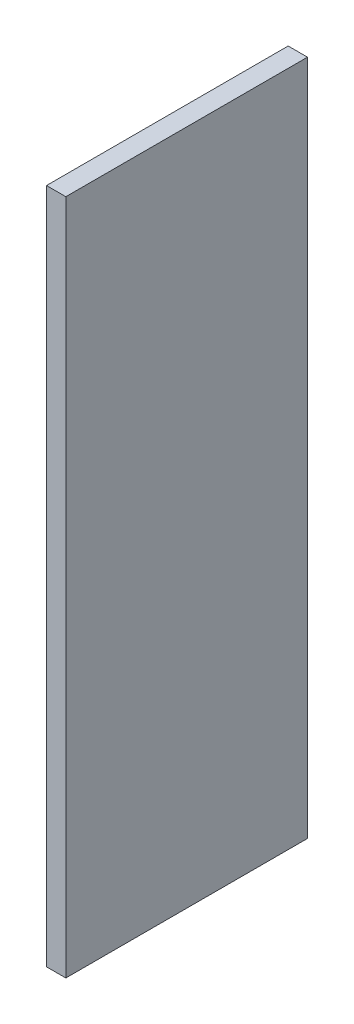
SolidWorks part; units mm, degrees
ref_plane "Front Plane" through (0, 0, 0) normal (0, 0, 1) x (1, 0, 0)
ref_plane "Top Plane" through (0, 0, 0) normal (0, 1, 0) x (1, 0, 0)
ref_plane "Right Plane" through (0, 0, 0) normal (1, 0, 0) x (0, 0, -1)
sketch "Sketch1" plane through (0, 0, 0) normal (0, 0, 1) x (1, 0, 0)
  line L1 (0, 0) -> (0.4, 0)
  line L2 (0, 0) -> (0, 14)
  line L3 (0, 14) -> (0.4, 14)
  line L4 (0.4, 0) -> (0.4, 14)
  dimension "D2" = 14
extrude "Boss-Extrude1" add sketch "Sketch1" along normal blind 5
equation "\"A.L\"= 0.07m"
equation "\"A.h\"= 0.007m"
equation "\"A.d\"= 0.005m"
equation "\"A.delta\"= 45.0001"
equation "\"A.w\"= 0m"
equation "\"A.v\"= 0.013m"
equation "\"A.s\"= 0.014m"
equation "\"A.t\"= 0.007m"
equation "\"B.L\"= 0.065m"
equation "\"B.h\"= 0.008m"
equation "\"B.s\"= 0.016m"
equation "\"B.t\"= 0.008m"
equation "\"C.h\"= 0.0065m"
equation "\"C.d\"= 0.005m"
equation "\"C.L\"= 0.05m"
equation "\"C.wmax\"= 0.003m"
equation "\"D.L\"= 0.06m"
equation "\"D.h\"= 0.008m"
equation "\"D.s\"= 0.012m"
equation "\"D.t\"= 0.008m"
equation "\"a_h\"= 0.0001m"
equation "\"a_d\"= 0.005m"
equation "\"a_L\"= 0.008m"
equation "\"b_h\"= 0.0004m"
equation "\"b_d\"= 0.005m"
equation "\"b_L\"= 0.008m"
equation "\"c_h\"= 0.0001m"
equation "\"c_d\"= 0.005m"
equation "\"c_L\"= 0.01m"
equation "\"d_h\"= 0.0001m"
equation "\"d_d\"= 0.005m"
equation "\"d_L\"= 0.01m"
equation "\"S.h\"= 0.015m"
equation "\"S.L\"= 0.09175m"
equation "\"D1@Sketch1\"=\"b_h\""
equation "\"D2@Sketch1\"=\"b_L\"+0.006"
equation "\"D1@Boss-Extrude1\"=\"b_d\""
